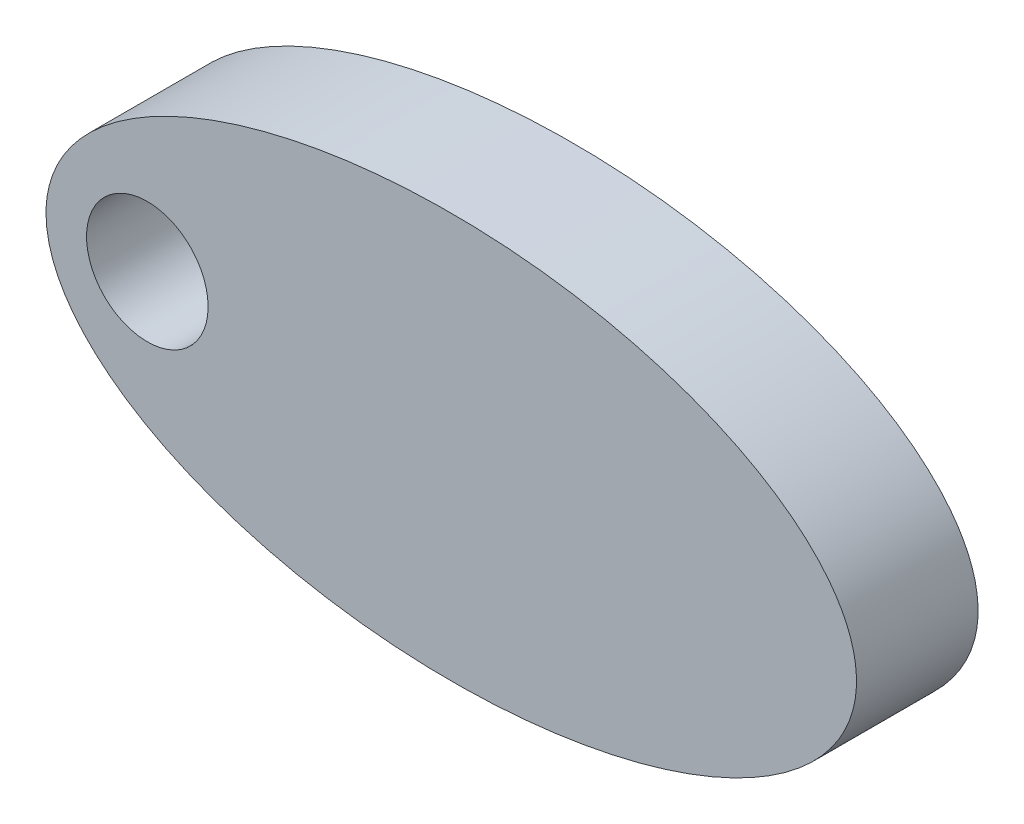
SolidWorks part; units mm, degrees
ref_plane "Front Plane" through (0, 0, 0) normal (0, 0, 1) x (1, 0, 0)
ref_plane "Top Plane" through (0, 0, 0) normal (0, 1, 0) x (1, 0, 0)
ref_plane "Right Plane" through (0, 0, 0) normal (1, 0, 0) x (0, 0, -1)
sketch "Sketch1" plane through (0, 0, 0) normal (0, 0, 1) x (1, 0, 0)
  circle A0 centre (-7.5, 0) radius 1.5
  ellipse E0 centre (0, 0) end of major axis (-10, 0) minor radius 5
  dimension "D1" = 3
  dimension "D3" = 7.5
extrude "Boss-Extrude1" add sketch "Sketch1" along normal blind 3
